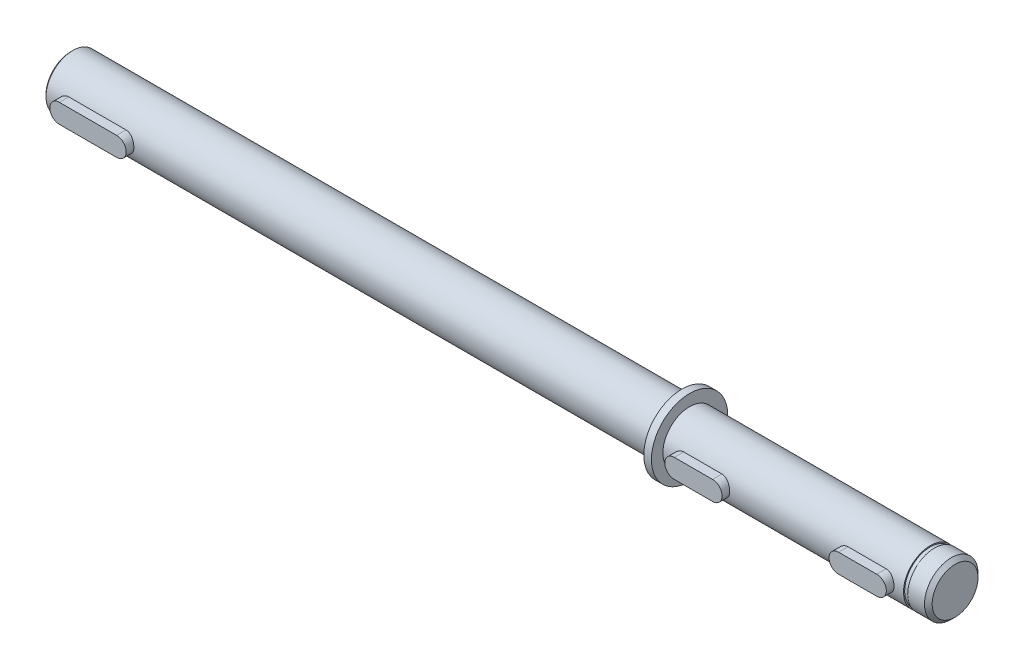
SolidWorks part; units mm, degrees
material "铸造合金钢"
ref_plane "前视基准面" through (0, 0, 0) normal (0, 0, 1) x (1, 0, 0)
ref_plane "上视基准面" through (0, 0, 0) normal (0, 1, 0) x (1, 0, 0)
ref_plane "右视基准面" through (0, 0, 0) normal (1, 0, 0) x (0, 0, -1)
sketch "草图1" plane through (0, 0, 0) normal (0, 0, 1) x (1, 0, 0)
  line L1 (-129, 0) -> (129, 0)
  line L2 (-129, 0) -> (-129, 6.5)
  line L3 (-128.5, 7) -> (31, 7)
  line L4 (31, 7) -> (31, 10)
  line L5 (31, 10) -> (33, 10)
  line L6 (33, 10) -> (33, 7)
  line L7 (129, 6) -> (128, 7)
  line L13 (-129, 6.5) -> (-128.5, 7)
  line L16 (128, 7) -> (33, 7)
  line L17 (129, 0) -> (129, 6)
  point P6 (-129, 7)
  point P13 (129, 7)
  dimension "D1" = 162
  dimension "D2" = 160
  dimension "D3" = 7
  dimension "D4" = 258
  dimension "D5" = 7
  dimension "D6" = 10
revolve "旋转1" add sketch "草图1" angle 360 about L1
sketch "草图2" plane through (0, 0, 0) normal (0, 0, 1) x (1, 0, 0)
  line L0 (123, 0) -> (108, 0) construction
  line L1 (123, -2.5) -> (108, -2.5)
  line L2 (123, 2.5) -> (108, 2.5)
  line L3 (0, 0) -> (0, 28.608) construction
  line L4 (129, -6) -> (129, 6) construction
  line L5 (-123, 0) -> (-108, 0) construction
  line L6 (-123, -2.5) -> (-108, -2.5)
  line L7 (-123, 2.5) -> (-108, 2.5)
  line L8 (38, 0) -> (48, 0) construction
  line L9 (38, 2.5) -> (48, 2.5)
  line L10 (38, -2.5) -> (48, -2.5)
  line L11 (33, -7) -> (33, 7) construction
  line L12 (123, 0) -> (108, 0) construction
  line L13 (123, -2.5) -> (108, -2.5)
  line L14 (123, 2.5) -> (108, 2.5)
  line L15 (-38, 0) -> (-48, 0) construction
  line L16 (-38, 2.5) -> (-48, 2.5)
  line L17 (-38, -2.5) -> (-48, -2.5)
  line L18 (81, 0) -> (91, 0) construction
  line L19 (81, 2.5) -> (91, 2.5)
  line L20 (81, -2.5) -> (91, -2.5)
  arc A0 (123, -2.5) -> (123, 2.5) centre (123, 0) ccw
  arc A1 (108, 2.5) -> (108, -2.5) centre (108, 0) ccw
  arc A2 (-123, -2.5) -> (-123, 2.5) centre (-123, 0) cw
  arc A3 (-108, 2.5) -> (-108, -2.5) centre (-108, 0) cw
  arc A4 (38, 2.5) -> (38, -2.5) centre (38, 0) ccw
  arc A5 (48, -2.5) -> (48, 2.5) centre (48, 0) ccw
  arc A6 (123, -2.5) -> (123, 2.5) centre (123, 0) ccw
  arc A7 (108, 2.5) -> (108, -2.5) centre (108, 0) ccw
  arc A8 (-38, 2.5) -> (-38, -2.5) centre (-38, 0) cw
  arc A9 (-48, -2.5) -> (-48, 2.5) centre (-48, 0) cw
  arc A10 (81, 2.5) -> (81, -2.5) centre (81, 0) ccw
  arc A11 (91, -2.5) -> (91, 2.5) centre (91, 0) ccw
  point P3 (115.5, 0)
  point P14 (-115.5, 0)
  point P21 (43, 0)
  point P36 (-43, 0)
  point P41 (86, 0)
  dimension "D1" = 2.5
  dimension "D4" = 2.5
  dimension "D8" = 2.5
  dimension "D2" = 6
  dimension "D3" = 15
  dimension "D5" = 10
  dimension "D6" = 5
  dimension "D7" = 10
  dimension "D9" = 33
extrude "凸台-拉伸1" add sketch "草图2" along normal blind 9 contours A3 L7 A2 L6 | L10 A5 L9 A4 | L2 A1 L1 A0 | L20 A11 L19 A10
sketch "草图3" plane through (129, 0, 0) normal (1, 0, 0) x (0, 0, -1)
  circle A0 centre (0, 0) radius 15
  dimension "D1" = 30
extrude "切除-拉伸1" cut sketch "草图3" against normal blind 26.5
hole_wizard "M6 螺纹孔1" positions "草图5" profile "草图4" tap size "M6" standard "GB"
sketch "草图5" plane through (-129, 0, 0) normal (-1, 0, 0) x (0, 0, 1)
  point P0 (0, 0)
sketch "草图4" plane through (-129, 0, 0) normal (0, 1, 0) x (0, 0, 1)
  line L0 (0, 0) -> (0, 18.5022)
  line L1 (0, 18.5022) -> (2.5, 17)
  line L2 (2.5, 17) -> (2.5, 0)
  line L5 (2.5, 0) -> (0, 0)
  line L10 (0, 18.5022) -> (-2.5, 17) construction
  line L11 (0, -6.35) -> (0, 107.95) construction
  dimension "螺纹孔钻头直径" = 5
  dimension "螺纹孔钻头深度" = 17
  dimension "导头角度" = 118
cosmetic thread "孔螺蚊线1" parameters "D1"=12, "D2"=6
chamfer "倒角1" distance 1 angle 45 1 edges at (102.5, 0, -7)
sketch "草图6" plane through (0, 0, 0) normal (0, 0, 1) x (1, 0, 0)
  line L0 (0, 0) -> (40.44, 0) construction
  line L1 (33, -7) -> (101.5, -7) construction
  line L2 (96, -7) -> (97.1, -7)
  line L3 (96, -7) -> (96, -6.7)
  line L4 (96, -6.7) -> (97.1, -6.7)
  line L5 (97.1, -7) -> (97.1, -6.7)
  line L6 (33, -7) -> (33, 7) construction
  dimension "D1" = 63
  dimension "D2" = 1.1
  dimension "D3" = 13.4
revolve "切除-旋转1" cut sketch "草图6" angle 360 about L0
